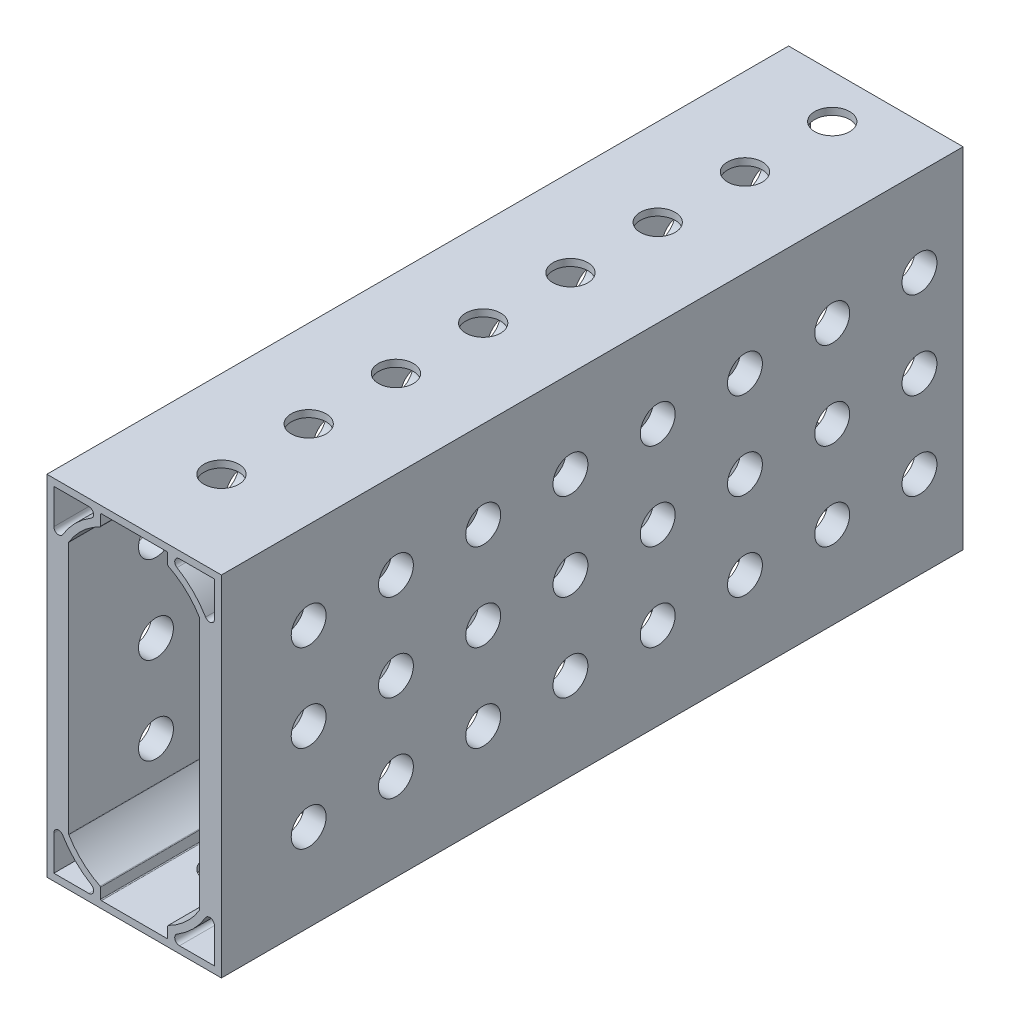
SolidWorks part; units mm, degrees
material "6061 Alloy"
ref_plane "Front Plane" through (0, 0, 0) normal (0, 0, 1) x (1, 0, 0)
ref_plane "Top Plane" through (0, 0, 0) normal (0, 1, 0) x (1, 0, 0)
ref_plane "Right Plane" through (0, 0, 0) normal (1, 0, 0) x (0, 0, -1)
other "Configuration Table"
ref_plane "Plane1" through (-12.7, 0, 0) normal (-1, 0, 0) x (0, -1, 0)
sketch "Sketch1" plane through (-12.7, 0, 0) normal (-1, 0, 0) x (0, -1, 0)
  line L0 (-25.4, -53.975) -> (25.4, -53.975)
  line L1 (25.4, -53.975) -> (25.4, 53.975)
  line L2 (25.4, 53.975) -> (-25.4, 53.975)
  line L3 (-25.4, 53.975) -> (-25.4, -53.975)
  line L4 (-25.4, -53.975) -> (25.4, 53.975) construction
  point P6 (0, 0)
  dimension "D1" = 50.8
  dimension "D2" = 107.95
extrude "Boss-Extrude1" add sketch "Sketch1" against normal blind 25.4
sketch "Sketch10" plane through (0, 0, 53.975) normal (0, 0, 1) x (1, 0, 0)
  line L0 (-11.684, 24.384) -> (-11.684, 19.2971)
  line L1 (-6.5971, 24.384) -> (-11.684, 24.384)
  line L2 (-12.7, -25.4) -> (-12.7, 25.4) construction
  line L18 (-12.7, -25.4) -> (-12.7, 25.4) construction
  line L19 (12.7, -25.4) -> (-12.7, -25.4) construction
  line L55 (0, 24.384) -> (-4.8895, 24.384)
  line L56 (-4.8895, 24.384) -> (-4.8895, 22.679)
  line L57 (-9.525, 18.4238) -> (-9.525, 0)
  line L70 (12.7, 25.4) -> (-12.7, 25.4) construction
  line L72 (12.7, 25.4) -> (-12.7, 25.4) construction
  line L73 (-9.525, 0) -> (0, 0)
  line L74 (0, 0) -> (0, 24.384)
  arc A0 (-11.684, 19.2971) -> (-10.3994, 18.9412) centre (-10.9924, 19.2971) ccw
  arc A1 (-10.3994, 18.9412) -> (-6.2412, 23.0994) centre (0, 12.7) cw
  arc A2 (-6.2412, 23.0994) -> (-6.5971, 24.384) centre (-6.5971, 23.6924) ccw
  arc A8 (-4.8895, 22.679) -> (-9.525, 18.4238) centre (0, 12.7) ccw
  dimension "D1" = 0.6916
  dimension "D2" = 12.1285
  dimension "D3" = 3.175
  dimension "D11" = 11.1125
  dimension "D12" = 1.016
  dimension "D4" = 1.016
  dimension "D5" = 2.3006
  dimension "D6" = 1.016
  dimension "D8" = 1.016
  dimension "D13" = 4.8895
extrude "Cut-Extrude9" cut sketch "Sketch10" against normal through all
mirror "Mirror1" about plane through (0, 0, 0) normal (0, 1, 0) of "Cut-Extrude9" second plane through (0, 0, 0) second plane normal (1, 0, 0)
sketch "Sketch17" plane through (12.7, 0, 0) normal (1, 0, 0) x (0, 0, -1)
  line L1 (-53.975, 25.4) -> (53.975, 25.4) construction
  line L2 (-53.975, -25.4) -> (-53.975, 25.4) construction
  circle A0 centre (-41.275, 12.7) radius 2.54
  dimension "D2" = 5.08
  dimension "D1" = 12.7
  dimension "D3" = 12.7
sketch "Sketch18" plane through (0, 25.4, 0) normal (0, 1, 0) x (1, 0, 0)
  line L1 (12.7, -53.975) -> (-12.7, -53.975) construction
  line L2 (12.7, -53.975) -> (12.7, 53.975) construction
  circle A0 centre (0, -41.275) radius 2.54
  dimension "D1" = 5.08
  dimension "D2" = 12.7
  dimension "D3" = 12.7
extrude "Cut-Extrude11" cut sketch "Sketch17" against normal through all and the other way through all
extrude "Cut-Extrude12" cut sketch "Sketch18" against normal through all
pattern_linear "LPattern1" count 9 spacing 12.7 along (0, 0, -1) of "Cut-Extrude12"
pattern_linear "LPattern2" count 9 spacing 12.7 along (0, 0, -1) count 3 spacing 12.7 along (0, -1, 0) of "Cut-Extrude11"
fillet "Fillet1" radius 0.127 12 edges at (-4.8895, -24.384, 0) (-4.8895, -22.679, 0) (-9.525, -18.4238, 0) (4.8895, -22.679, 0) (4.8895, -24.384, 0) (9.525, -18.4238, 0) (-4.8895, 22.679, 0) (-4.8895, 24.384, 0) (-9.525, 18.4238, 0) (4.8895, 24.384, 0) (4.8895, 22.679, 0) (9.525, 18.4238, 0)
equation "\"Length\"= 4.25"
equation "\"D2@Sketch1\"=\"Length\""
